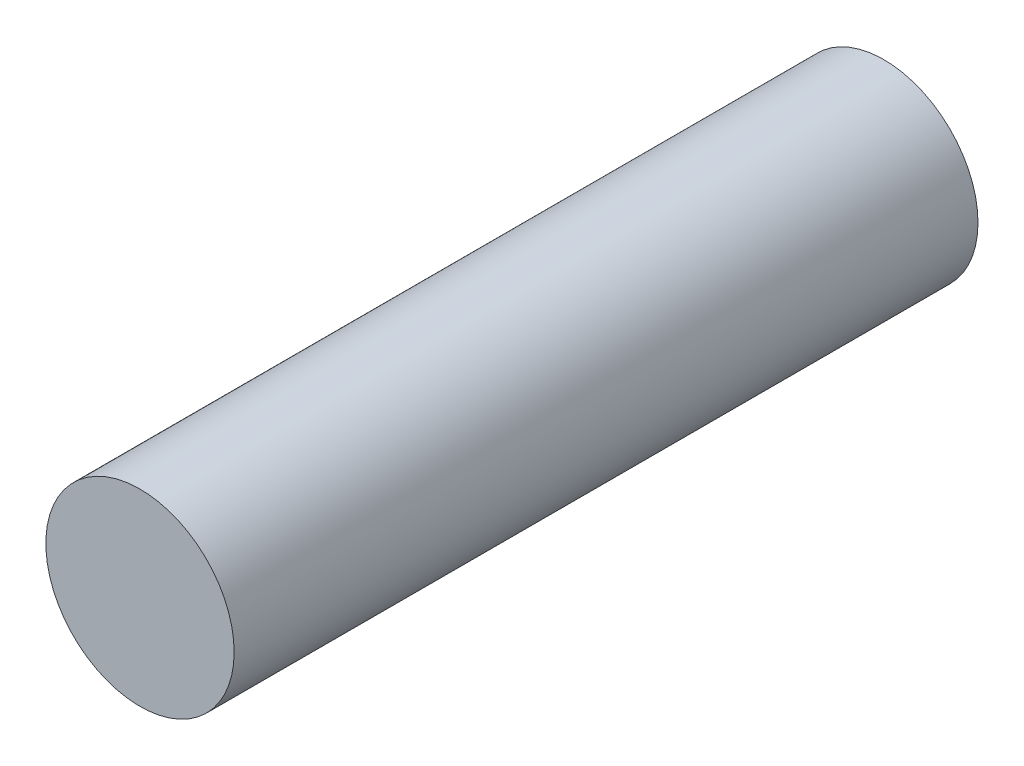
SolidWorks part; units mm, degrees
ref_plane "Front Plane" through (0, 0, 0) normal (0, 0, 1) x (1, 0, 0)
ref_plane "Top Plane" through (0, 0, 0) normal (0, 1, 0) x (1, 0, 0)
ref_plane "Right Plane" through (0, 0, 0) normal (1, 0, 0) x (0, 0, -1)
sketch "Sketch1" plane through (0, 0, 0) normal (0, 0, 1) x (1, 0, 0)
  circle A0 centre (-10.0166, -10.0166) radius 3.7971
extrude "Boss-Extrude1" add sketch "Sketch1" along normal blind 30
